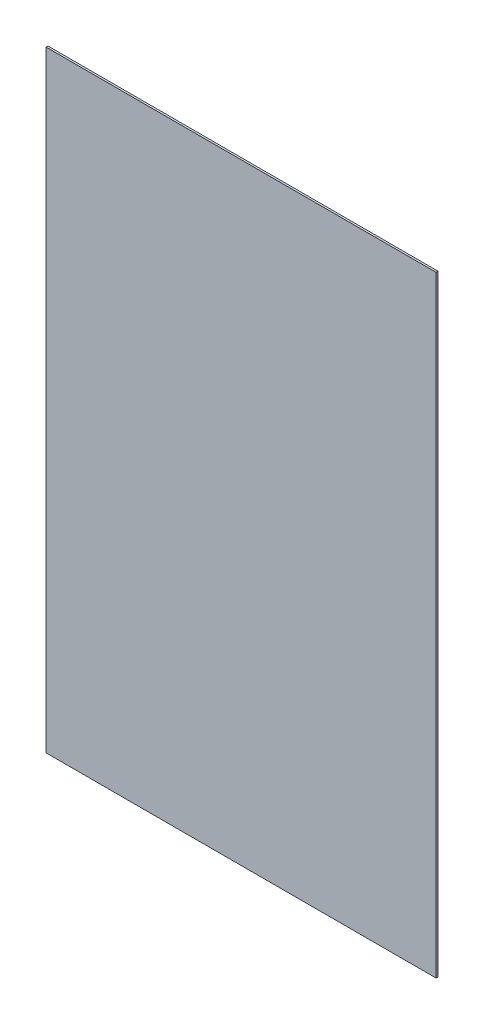
SolidWorks part; units mm, degrees
ref_plane "Front Plane" through (0, 0, 0) normal (0, 0, 1) x (1, 0, 0)
ref_plane "Top Plane" through (0, 0, 0) normal (0, 1, 0) x (1, 0, 0)
ref_plane "Right Plane" through (0, 0, 0) normal (1, 0, 0) x (0, 0, -1)
sketch "Sketch1" plane through (0, 0, 0) normal (0, 0, 1) x (1, 0, 0)
  line L1 (500, 783.875) -> (-500, 783.875)
  line L2 (500, 783.875) -> (500, -783.875)
  line L3 (500, -783.875) -> (-500, -783.875)
  line L4 (-500, 783.875) -> (-500, -783.875)
  line L5 (500, 783.875) -> (-500, -783.875) construction
  line L6 (500, -783.875) -> (-500, 783.875) construction
  point P0 (0, 0)
  dimension "D1" = 1000
  dimension "D2" = 1567.75
extrude "Boss-Extrude1" add sketch "Sketch1" along normal mid plane 5
